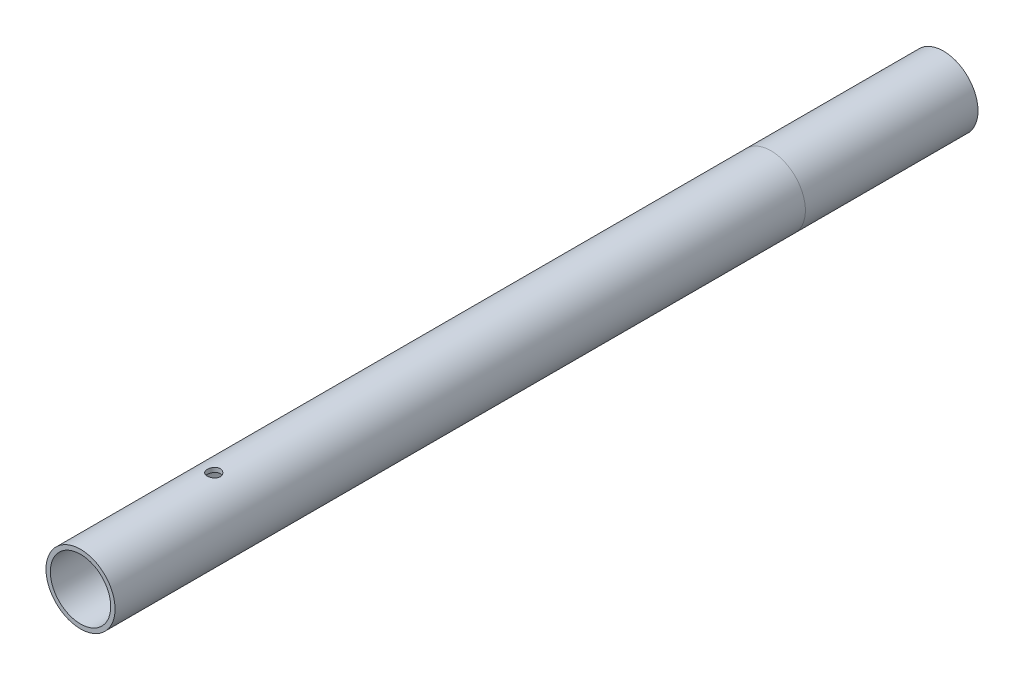
SolidWorks part; units mm, degrees
material "Plain Carbon Steel"
ref_plane "Ön Düzlem" through (0, 0, 0) normal (0, 0, 1) x (1, 0, 0)
ref_plane "Üst Düzlem" through (0, 0, 0) normal (0, 1, 0) x (1, 0, 0)
ref_plane "Sağ Düzlem" through (0, 0, 0) normal (1, 0, 0) x (0, 0, -1)
sketch "Sketch1" plane through (0, 0, 0) normal (0, 0, 1) x (1, 0, 0)
  circle A0 centre (0, 0) radius 8
  circle A2 centre (0, 0) radius 7
  dimension "D1" = 16
  dimension "D2" = 1
extrude "Boss-Extrude1" add sketch "Sketch1" along normal blind 200
sketch "Sketch2" plane through (0, 0, 0) normal (0, 1, 0) x (1, 0, 0)
  line L0 (-15, -40) -> (15, -40)
  point P4 (0, -40)
  dimension "D1" = 40
  dimension "D2" = 30
split line "Split Line2"
sketch "Sketch3" plane through (0, 0, 0) normal (0, 1, 0) x (1, 0, 0)
  line L1 (-8, -200) -> (8, -200) construction
  circle A2 centre (0, -169.13) radius 1.5
  dimension "D1" = 3
  dimension "D2" = 30.87
extrude "Cut-Extrude1" cut sketch "Sketch3" against normal through all both and the other way through all
equation "\"motor_r\"= 35 / 2mm"
equation "\"boru_d\"= 16mm"
equation "\"D1@Sketch1\"=\"boru_d\""
